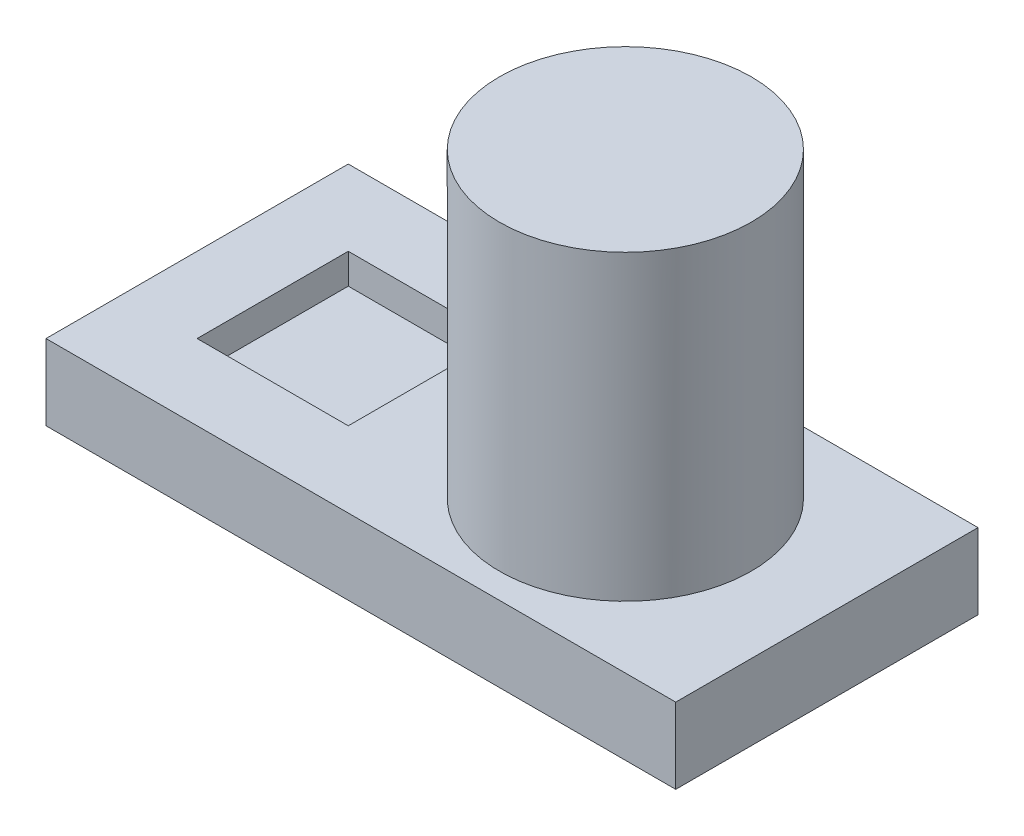
SolidWorks part; units mm, degrees
ref_plane "Front" through (0, 0, 0) normal (0, 0, 1) x (1, 0, 0)
ref_plane "Top" through (0, 0, 0) normal (0, 1, 0) x (1, 0, 0)
ref_plane "Right" through (0, 0, 0) normal (1, 0, 0) x (0, 0, -1)
sketch "Sketch1" plane through (0, 0, 0) normal (0, 1, 0) x (1, 0, 0)
  line L1 (0, 0) -> (125, 0)
  line L2 (0, 0) -> (0, 60)
  line L3 (0, 60) -> (125, 60)
  line L4 (125, 0) -> (125, 60)
  dimension "D1" = 125
  dimension "D2" = 60
extrude "Extrude1" add sketch "Sketch1" along normal blind 15
sketch "Sketch2" plane through (0, 15, 0) normal (0, 1, 0) x (-1, 0, 0)
  circle A0 centre (-85, -30) radius 25
extrude "Extrude2" add sketch "Sketch2" along normal blind 60
sketch "Sketch3" plane through (0, 15, 0) normal (0, 1, 0) x (-1, 0, 0)
  line L3 (-15, -45) -> (-15, -15)
  line L4 (-15, -15) -> (-45, -15)
  line L5 (-45, -45) -> (-45, -15)
  line L6 (-15, -45) -> (-45, -45)
  line L7 (-15, -15) -> (-55.9323, -15) construction
  line L8 (-15, -45) -> (-55.9323, -45) construction
  line L9 (-45, -60) -> (-45, -15) construction
  line L10 (-15, -60) -> (-15, -15) construction
extrude "Cut-Extrude1" cut sketch "Sketch3" against normal blind 6
